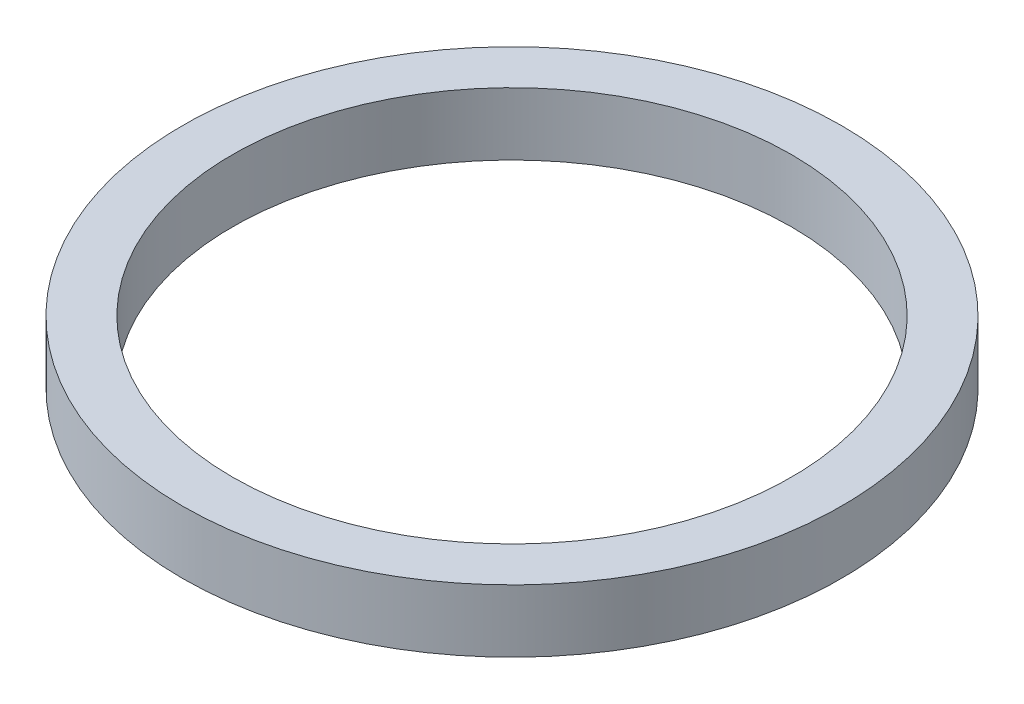
SolidWorks part; units mm, degrees
ref_plane "Front Plane" through (0, 0, 0) normal (0, 0, 1) x (1, 0, 0)
ref_plane "Top Plane" through (0, 0, 0) normal (0, 1, 0) x (1, 0, 0)
ref_plane "Right Plane" through (0, 0, 0) normal (1, 0, 0) x (0, 0, -1)
sketch "Sketch1" plane through (0, 0, 0) normal (0, 0, 1) x (1, 0, 0)
  line L0 (0, 0) -> (0, 13.6387) construction
  line L1 (-14.1605, 0) -> (0, 0) construction
  line L2 (-16.7005, 1.5875) -> (-14.1605, 1.5875)
  line L3 (-16.7005, 1.5875) -> (-16.7005, -1.5875)
  line L4 (-16.7005, -1.5875) -> (-14.1605, -1.5875)
  line L5 (-14.1605, 1.5875) -> (-14.1605, -1.5875)
  dimension "D1" = 2.54
  dimension "D2" = 33.401
  dimension "D3" = 3.175
revolve "Revolve1" add sketch "Sketch1" angle 360 about L0
